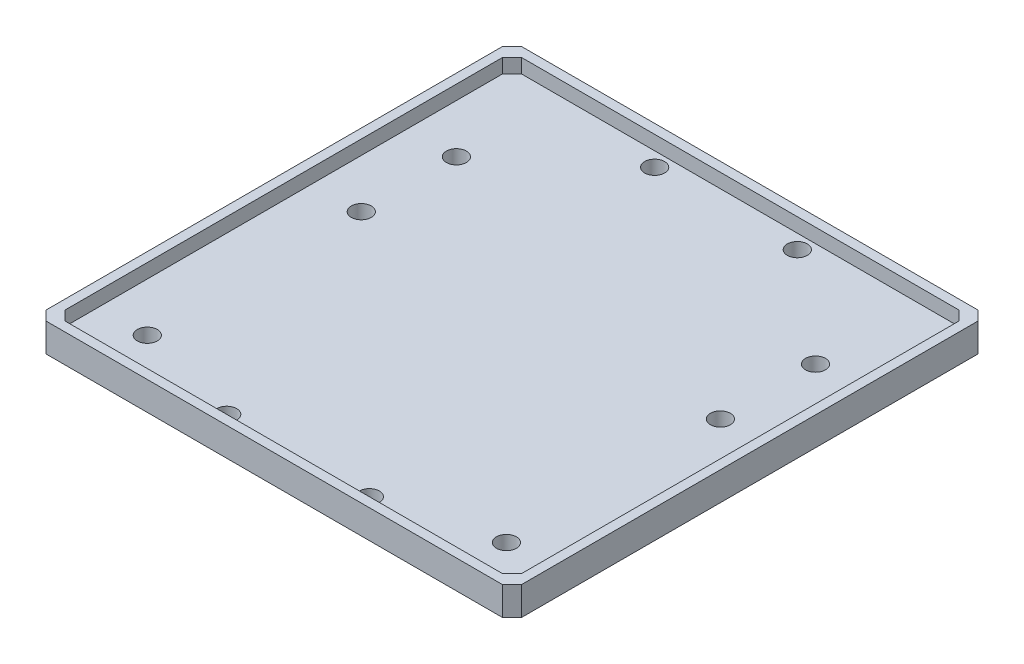
SolidWorks part; units mm, degrees
ref_plane "Front Plane" through (0, 0, 0) normal (0, 0, 1) x (1, 0, 0)
ref_plane "Top Plane" through (0, 0, 0) normal (0, 1, 0) x (1, 0, 0)
ref_plane "Right Plane" through (0, 0, 0) normal (1, 0, 0) x (0, 0, -1)
sketch "Sketch4" plane through (0, 0, 0) normal (0, 1, 0) x (1, 0, 0)
  line L3 (89.4442, -163.4248) -> (-10.5558, -163.4248)
  line L5 (89.4442, -63.4248) -> (-10.5558, -63.4248)
  line L6 (-10.5558, -163.4248) -> (-10.5558, -63.4248)
  line L7 (89.4442, -163.4248) -> (89.4442, -63.4248)
  circle A0 centre (1.6848, -87.3604) radius 2.1
  circle A1 centre (1.6848, -107.3604) radius 2.1
  circle A2 centre (1.6848, -152.3604) radius 2.1
  circle A3 centre (77.2035, -87.3604) radius 2.1
  circle A4 centre (77.2035, -107.3604) radius 2.1
  circle A5 centre (77.2035, -152.3604) radius 2.1
  circle A8 centre (54.4442, -158.4248) radius 2.1
  circle A9 centre (24.4442, -158.4248) radius 2.1
  circle A10 centre (54.4442, -68.4248) radius 2.1
  circle A11 centre (24.4442, -68.4248) radius 2.1
  dimension "D1" = 100
sketch "Sketch6" plane through (0, 0, 0) normal (0, 1, 0) x (1, 0, 0)
  line L0 (39.4442, -63.4248) -> (39.4442, -163.4248) construction
  line L1 (-10.5558, -63.4248) -> (89.4442, -63.4248)
  line L2 (-10.5558, -63.4248) -> (-10.5558, -163.4248)
  line L3 (-10.5558, -163.4248) -> (89.4442, -163.4248)
  line L4 (89.4442, -63.4248) -> (89.4442, -163.4248)
  circle A0 centre (1.6848, -87.3604) radius 2.1
  circle A1 centre (1.6848, -107.3604) radius 2.1
  circle A2 centre (1.6848, -152.3604) radius 2.1
  circle A3 centre (24.4442, -158.4248) radius 2.1
  circle A4 centre (24.4442, -68.4248) radius 2.1
  circle A5 centre (54.4442, -158.4248) radius 2.1
  circle A6 centre (77.2035, -152.3604) radius 2.1
  circle A7 centre (77.2035, -107.3604) radius 2.1
  circle A8 centre (77.2035, -87.3604) radius 2.1
  circle A9 centre (54.4442, -68.4248) radius 2.1
extrude "Boss-Extrude2" add sketch "Sketch6" along normal blind 3
sketch "Sketch7" plane through (0, 3, 0) normal (0, 1, 0) x (1, 0, 0)
  line L0 (89.4442, -63.4248) -> (-10.5558, -63.4248) construction
  line L1 (-10.5558, -163.4248) -> (-8.5558, -163.4248)
  line L2 (-10.5558, -163.4248) -> (-10.5558, -63.4248)
  line L3 (-10.5558, -63.4248) -> (-8.5558, -63.4248)
  line L4 (-8.5558, -163.4248) -> (-8.5558, -63.4248)
  line L5 (39.4442, -63.4248) -> (39.4442, -163.4248) construction
  line L6 (-10.5558, -163.4248) -> (89.4442, -163.4248) construction
  line L7 (89.4442, -63.4248) -> (87.4442, -63.4248)
  line L8 (87.4442, -163.4248) -> (87.4442, -63.4248)
  line L9 (89.4442, -163.4248) -> (87.4442, -163.4248)
  line L10 (89.4442, -163.4248) -> (89.4442, -63.4248)
  line L12 (-8.5558, -63.4248) -> (87.4442, -63.4248)
  line L13 (-8.5558, -63.4248) -> (-8.5558, -65.4248)
  line L14 (-8.5558, -65.4248) -> (87.4442, -65.4248)
  line L15 (87.4442, -63.4248) -> (87.4442, -65.4248)
  line M16 (-10.5558, -163.4248) -> (89.4442, -163.4248)
  line M17 (89.4442, -163.4248) -> (89.4442, -63.4248)
  line M18 (89.4442, -63.4248) -> (-10.5558, -63.4248)
  dimension "D1" = 2
  dimension "D2" = 0
  dimension "D3" = 2
extrude "Boss-Extrude3" add sketch "Sketch7" along normal blind 3 contours L5 L14 L8 M18 | L5 L12 L4 L14 | L8 M16 M17 M18
sketch "Sketch8" plane through (0, 3, 0) normal (0, 1, 0) x (1, 0, 0)
  line L0 (87.4442, -163.4248) -> (87.4442, -65.4248) construction
  line L1 (-8.5558, -163.4248) -> (87.4442, -163.4248)
  line L2 (-8.5558, -163.4248) -> (-8.5558, -161.4248)
  line L3 (-8.5558, -161.4248) -> (87.4442, -161.4248)
  line L4 (87.4442, -163.4248) -> (87.4442, -161.4248)
  dimension "D1" = 2
extrude "Boss-Extrude4" add sketch "Sketch8" along normal blind 3
chamfer "Chamfer1" distance 2 angle 45 4 edges at (-10.5558, 3, 63.4248) (-10.5558, 3, 163.4248) (89.4442, 3, 163.4248) (89.4442, 3, 63.4248)
sketch "Sketch9" plane through (0, 3, 0) normal (0, 1, 0) x (1, 0, 0)
  line L0 (-6.5558, -65.4248) -> (-8.5558, -67.4248)
  line L1 (-8.5558, -65.4248) -> (87.4442, -65.4248) construction
  line L2 (-8.5558, -161.4248) -> (-8.5558, -65.4248) construction
  line L3 (-8.5558, -67.4248) -> (-8.5558, -65.4248)
  line L4 (-8.5558, -65.4248) -> (-6.5558, -65.4248)
  line L5 (39.4442, -65.4248) -> (39.4442, -76.8168) construction
  line L6 (87.4442, -113.4248) -> (79.7492, -113.4248) construction
  line L7 (87.4442, -161.4248) -> (87.4442, -65.4248) construction
  line L8 (87.4442, -67.4248) -> (87.4442, -65.4248)
  line L9 (85.4442, -65.4248) -> (87.4442, -67.4248)
  line L10 (87.4442, -65.4248) -> (85.4442, -65.4248)
  line L11 (85.4442, -161.4248) -> (87.4442, -159.4248)
  line L12 (87.4442, -161.4248) -> (85.4442, -161.4248)
  line L13 (87.4442, -159.4248) -> (87.4442, -161.4248)
  line L14 (-8.5558, -159.4248) -> (-8.5558, -161.4248)
  line L15 (-6.5558, -161.4248) -> (-8.5558, -159.4248)
  line L16 (-8.5558, -161.4248) -> (-6.5558, -161.4248)
  dimension "D1" = 2
  dimension "D2" = 2
extrude "Boss-Extrude5" add sketch "Sketch9" along normal blind 3
